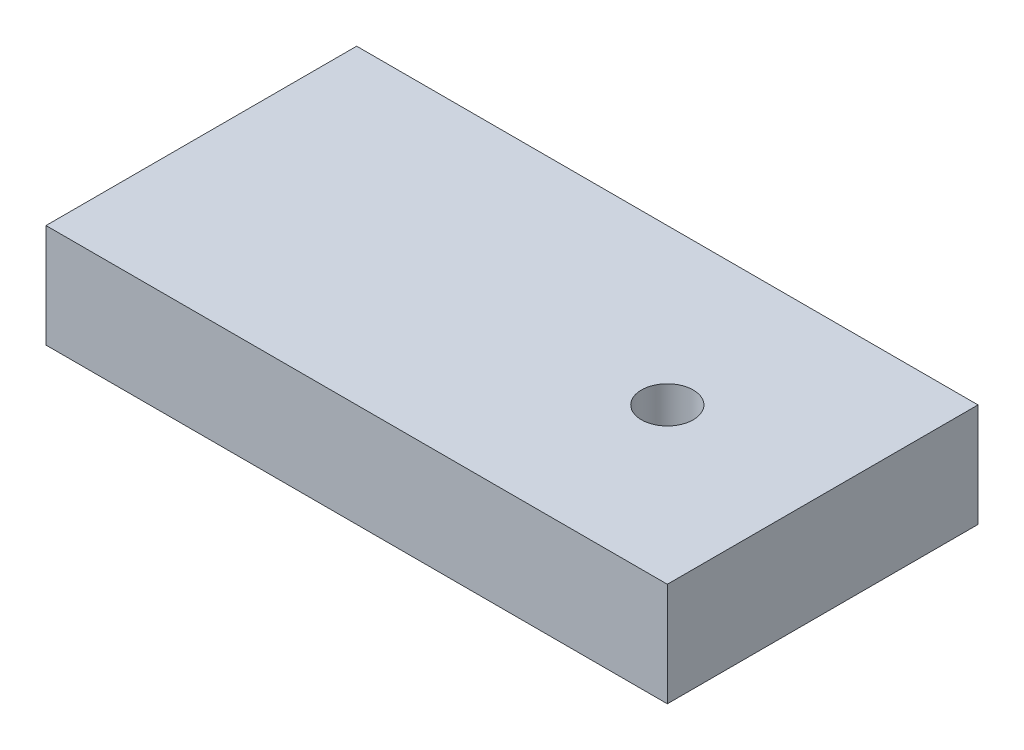
SolidWorks part; units mm, degrees
ref_plane "Front Plane" through (0, 0, 0) normal (0, 0, 1) x (1, 0, 0)
ref_plane "Top Plane" through (0, 0, 0) normal (0, 1, 0) x (1, 0, 0)
ref_plane "Right Plane" through (0, 0, 0) normal (1, 0, 0) x (0, 0, -1)
sketch "Sketch1" plane through (0, 0, 0) normal (0, 1, 0) x (1, 0, 0)
  line L1 (0, 0) -> (76.2, 0)
  line L2 (0, 0) -> (0, 38.1)
  line L3 (0, 38.1) -> (76.2, 38.1)
  line L4 (76.2, 0) -> (76.2, 38.1)
extrude "Boss-Extrude1" add sketch "Sketch1" along normal blind 12.7
sketch "Sketch2" plane through (0, 0, 0) normal (0, -1, 0) x (1, 0, 0)
  line L0 (76.2, 0) -> (76.2, -38.1) construction
  circle A0 centre (57.15, -19.05) radius 3.175
  circle A1 centre (74.984, -22.4671) radius 3.175 construction
  point P6 (76.2, -19.05)
  dimension "D1" = 19.05
extrude "Cut-Extrude1" cut sketch "Sketch2" against normal through all
sketch "Sketch3" plane through (0, 0, 0) normal (0, -1, 0) x (1, 0, 0)
  circle A0 centre (57.15, -19.05) radius 6.35
  dimension "D1" = 12.7
extrude "Cut-Extrude2" cut sketch "Sketch3" against normal blind 3
